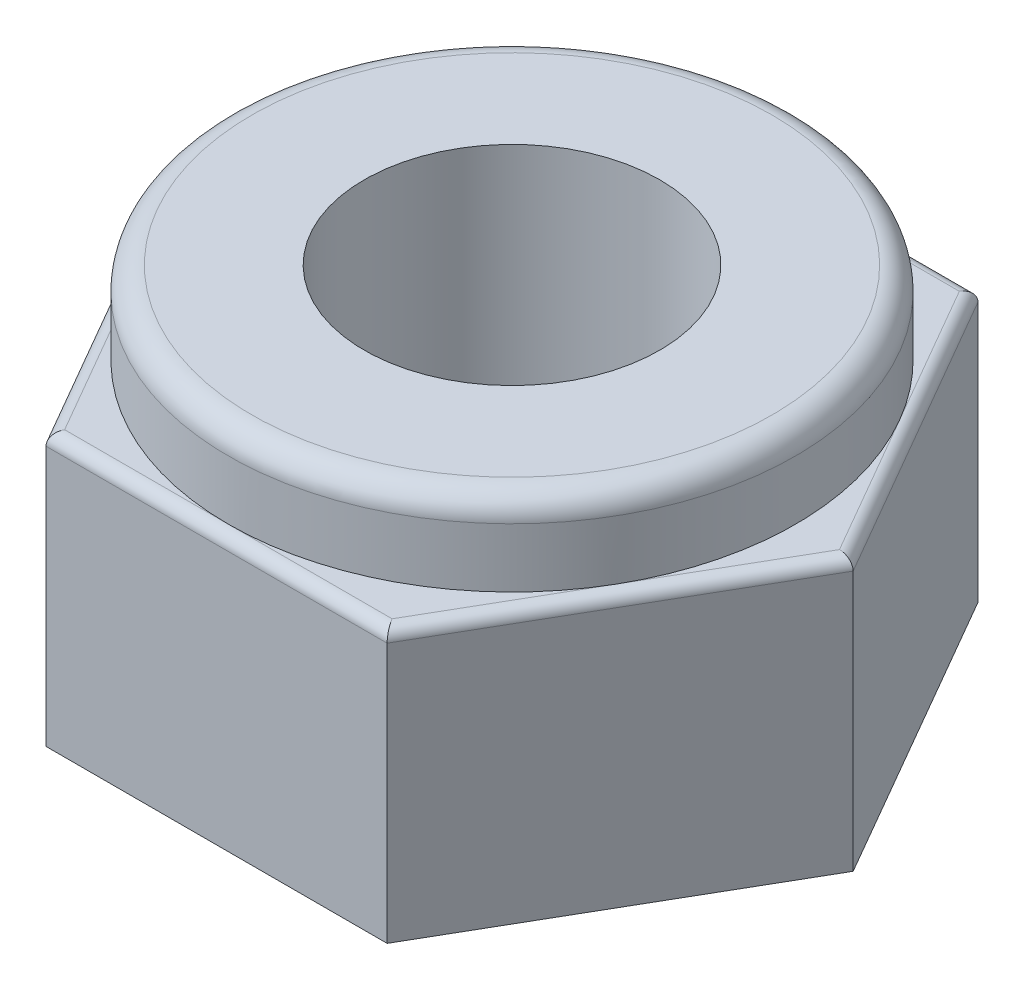
SolidWorks part; units mm, degrees
material "AISI 304"
ref_plane "前视基准面" through (0, 0, 0) normal (0, 0, 1) x (1, 0, 0)
ref_plane "上视基准面" through (0, 0, 0) normal (0, 1, 0) x (1, 0, 0)
ref_plane "右视基准面" through (0, 0, 0) normal (1, 0, 0) x (0, 0, -1)
sketch "草图1" plane through (0, 0, 0) normal (0, 1, 0) x (1, 0, 0)
  line L1 (1.4434, -2.5) -> (2.8868, 0)
  line L2 (2.8868, 0) -> (1.4434, 2.5)
  line L3 (1.4434, 2.5) -> (-1.4434, 2.5)
  line L4 (-1.4434, 2.5) -> (-2.8868, 0)
  line L5 (-2.8868, 0) -> (-1.4434, -2.5)
  line L6 (-1.4434, -2.5) -> (1.4434, -2.5)
  circle A0 centre (0, 0) radius 2.5 construction
  dimension "D1" = 5
extrude "凸台-拉伸1" add sketch "草图1" along normal blind 2.3
fillet "圆角1" radius 0.1 6 edges at (-2.1651, 2.3, 1.25) (-2.1651, 2.3, -1.25) (0, 2.3, -2.5) (2.1651, 2.3, -1.25) (2.1651, 2.3, 1.25) (0, 2.3, 2.5)
sketch "草图2" plane through (0, 0, 0) normal (0, -1, 0) x (1, 0, 0)
  line L0 (-1.3856, 2.4) -> (1.3856, 2.4) construction
  circle A0 centre (0, 0) radius 2.4
extrude "凸台-拉伸2" add sketch "草图2" against normal blind 3
fillet "圆角2" radius 0.2 1 edges at (0, 3, -2.4)
sketch "草图3" plane through (0, 0, 0) normal (0, -1, 0) x (1, 0, 0)
  circle A0 centre (0, 0) radius 1.25
  dimension "D1" = 2.5
extrude "切除-拉伸1" cut sketch "草图3" against normal blind 12.8
